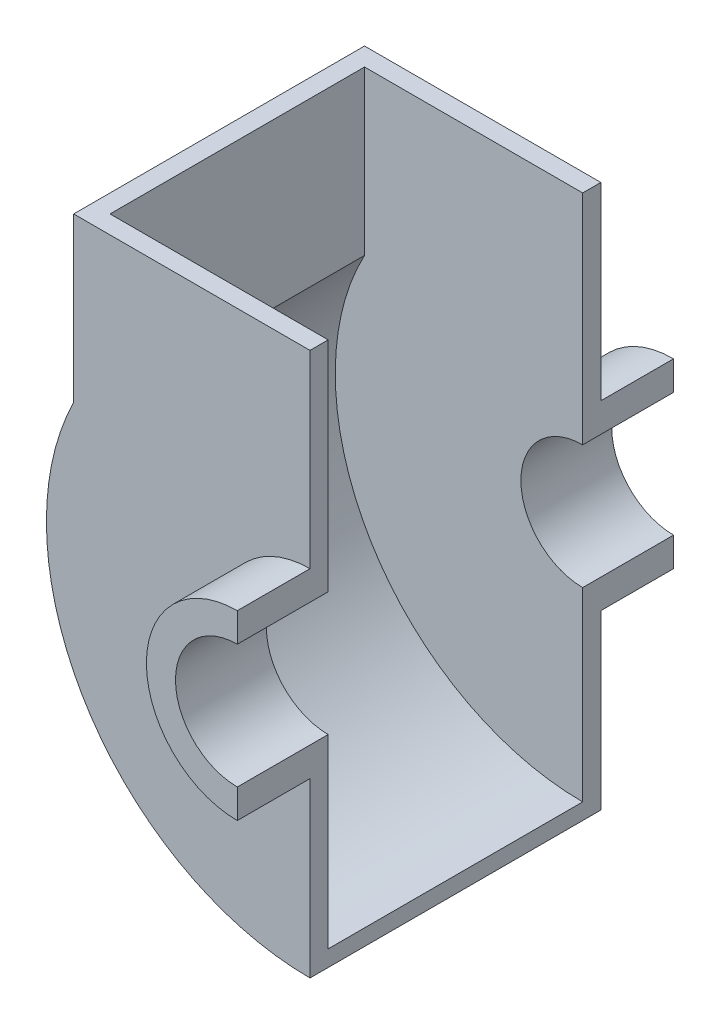
SolidWorks part; units mm, degrees
ref_plane "Front Plane" through (0, 0, 0) normal (0, 0, 1) x (1, 0, 0)
ref_plane "Top Plane" through (0, 0, 0) normal (0, 1, 0) x (1, 0, 0)
ref_plane "Right Plane" through (0, 0, 0) normal (1, 0, 0) x (0, 0, -1)
sketch "Sketch1" plane through (0, 0, 0) normal (0, 0, 1) x (1, 0, 0)
  line L0 (-40.1957, 0) -> (45.559, 0) construction
  line L1 (0, -31.7136) -> (0, 32.0443) construction
  line L2 (0, 25) -> (0, 17)
  line L3 (0, -17) -> (0, -25)
  arc A0 (0, 25) -> (0, -25) centre (0, 0) ccw
  arc A1 (0, 17) -> (0, -17) centre (0, 0) ccw
  dimension "D1" = 50
  dimension "D2" = 34
extrude "Boss-Extrude1" add sketch "Sketch1" along normal blind 20 and the other way blind 5
sketch "Sketch2" plane through (0, 0, 0) normal (0, 0, 1) x (1, 0, 0)
  line L0 (0, 25) -> (0, 77)
  line L1 (0, 77) -> (-65, 77)
  line L2 (0, -25) -> (0, -72.5)
  line L3 (-65, 77) -> (-65, 32.1131)
  arc A0 (-65, 32.1131) -> (0, -72.5) centre (0, 0) ccw
  arc A3 (0, 25) -> (0, -25) centre (0, 0) ccw
  dimension "D1" = 145
  dimension "D4" = 25
  dimension "D2" = 52
  dimension "D3" = 65
extrude "Boss-Extrude3" add sketch "Sketch2" against normal blind 5
ref_plane "Plane2" through (0, 0, -40) normal (0, 0, 1) x (1, 0, 0)
mirror "Mirror7" about plane through (0, 0, -40) normal (0, 0, 1) of bodies 103
sketch "Sketch3" plane through (0, 0, 0) normal (0, 0, 1) x (1, 0, 0)
  line L0 (-65, 32.1131) -> (-65, 77)
  line L1 (-65, 77) -> (-60, 77)
  line L2 (0, 77) -> (-65, 77) construction
  line L5 (-60, 77) -> (-60, 32.1131)
  line L6 (0, -72.5) -> (0, -68.0533)
  arc A3 (-65, 32.1131) -> (0, -72.5) centre (0, 0) ccw
  arc A4 (-60, 32.1131) -> (0, -68.0533) centre (0, 0) ccw
  dimension "D1" = 5
extrude "Boss-Extrude4" add sketch "Sketch3" against normal up to surface (75 mm away) up to face at (-29.3468, 15.924, -75)
